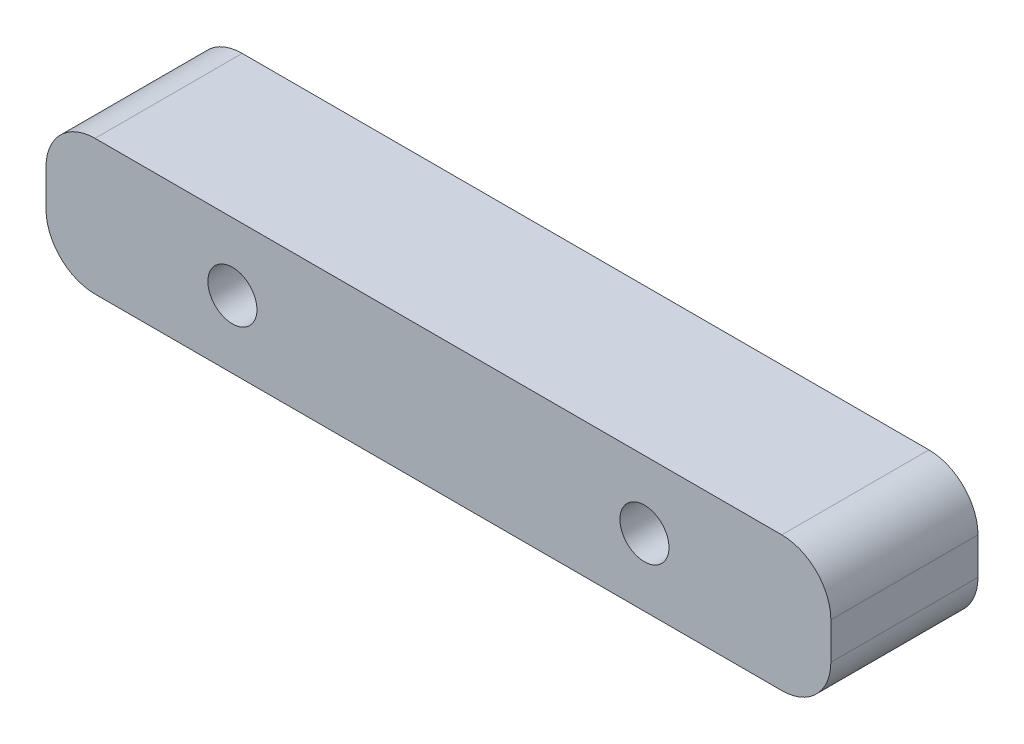
SolidWorks part; units mm, degrees
material "Custom Plastic"
ref_plane "Front Plane" through (0, 0, 0) normal (0, 0, 1) x (1, 0, 0)
ref_plane "Top Plane" through (0, 0, 0) normal (0, 1, 0) x (1, 0, 0)
ref_plane "Right Plane" through (0, 0, 0) normal (1, 0, 0) x (0, 0, -1)
sketch "Sketch1" plane through (0, 0, 0) normal (0, 0, 1) x (1, 0, 0)
  line L1 (-35, 6.875) -> (35, 6.875)
  line L2 (-40, 1.875) -> (-40, -1.875)
  line L3 (-35, -6.875) -> (35, -6.875)
  line L4 (40, 1.875) -> (40, -1.875)
  line L5 (-40, 6.875) -> (40, -6.875) construction
  line L6 (-40, -6.875) -> (40, 6.875) construction
  arc A0 (35, -6.875) -> (40, -1.875) centre (35, -1.875) ccw
  arc A1 (-40, -1.875) -> (-35, -6.875) centre (-35, -1.875) ccw
  arc A2 (40, 1.875) -> (35, 6.875) centre (35, 1.875) ccw
  arc A3 (-40, 1.875) -> (-35, 6.875) centre (-35, 1.875) cw
  point P0 (0, 0)
  dimension "D3" = 5
  dimension "D1" = 13.75
  dimension "D2" = 80
extrude "Boss-Extrude1" add sketch "Sketch1" along normal blind 15
sketch "Sketch2" plane through (0, 0, 15) normal (0, 0, 1) x (1, 0, 0)
  circle A0 centre (-21, 0) radius 2.5
  circle A1 centre (21, 0) radius 2.5
  dimension "D1" = 5
  dimension "D2" = 42
  dimension "D3" = 21
extrude "Cut-Extrude1" cut sketch "Sketch2" against normal through all
